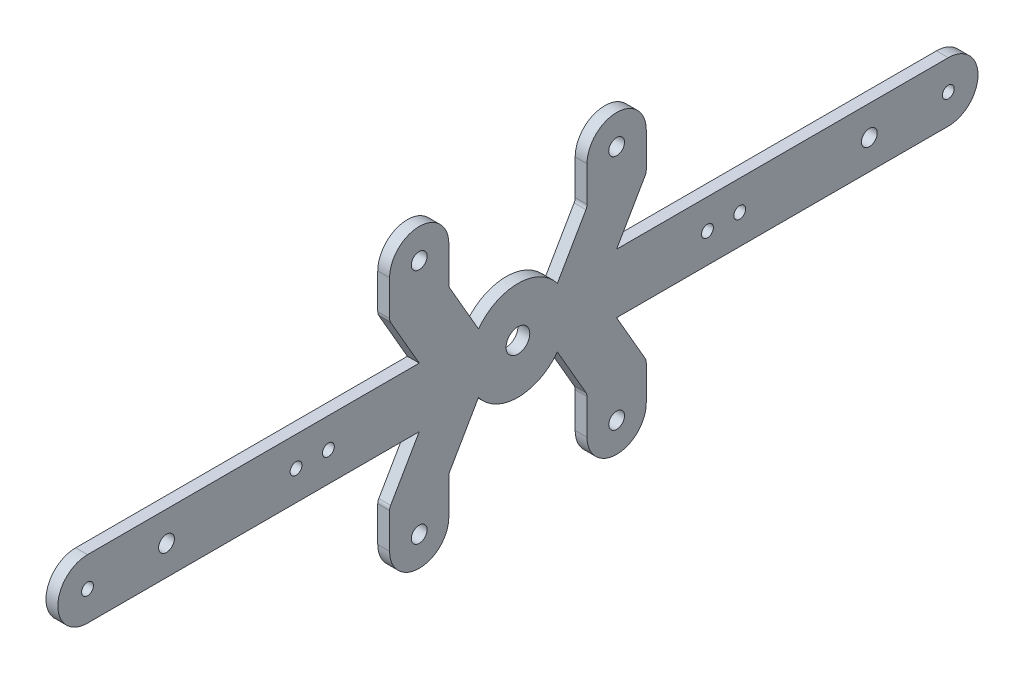
SolidWorks part; units mm, degrees
material "Acrylic (Medium-high impact)"
ref_plane "Front Plane" through (0, 0, 0) normal (0, 0, 1) x (1, 0, 0)
ref_plane "Top Plane" through (0, 0, 0) normal (0, 1, 0) x (1, 0, 0)
ref_plane "Right Plane" through (0, 0, 0) normal (1, 0, 0) x (0, 0, -1)
sketch "Sketch1" plane through (0, 0, 0) normal (1, 0, 0) x (0, 0, -1)
  line L0 (0, 0) -> (-114.2997, 0) construction
  line L1 (125, -45) -> (-125, -45)
  line L2 (125, -45) -> (125, 45)
  line L3 (125, 45) -> (-125, 45)
  line L4 (-125, -45) -> (-125, 45)
  line L5 (125, -45) -> (-125, 45) construction
  line L6 (125, 45) -> (-125, -45) construction
  point P0 (0, 0)
  dimension "D1" = 250
  dimension "D2" = 90
extrude "Boss-Extrude1" add sketch "Sketch1" along normal blind 3
sketch "Sketch2" plane through (3, 0, 0) normal (1, 0, 0) x (0, 0, -1)
  circle A0 centre (0, 0) radius 3
  circle A1 centre (-48, 0) radius 1.5
  circle A2 centre (-89, 0) radius 2
  circle A3 centre (-109, 0) radius 1.5
  circle A4 centre (-56.18, 0) radius 1.5
  dimension "D1" = 4
  dimension "D2" = 3
  dimension "D3" = 6
  dimension "D4" = 20
  dimension "D7" = 3
  dimension "D5" = 41
  dimension "D6" = 48
  dimension "D8" = 32.82
extrude "Cut-Extrude1" cut sketch "Sketch2" against normal through all
sketch "Sketch3" plane through (3, 0, 0) normal (1, 0, 0) x (0, 0, -1)
  line L0 (0, 55) -> (0, -55) construction
  line L1 (55, 0) -> (-55, 0) construction
  circle A0 centre (-25, 30) radius 2
  dimension "D1" = 4
  dimension "D2" = 25
  dimension "D3" = 30
extrude "Cut-Extrude2" cut sketch "Sketch3" against normal through all
sketch "Sketch4" plane through (3, 0, 0) normal (1, 0, 0) x (0, 0, -1)
  line L2 (-125, 1.9956) -> (-125, 45)
  line L5 (-125, 45) -> (0, 45)
  line L6 (125, 45) -> (-125, 45) construction
  line L13 (-116.5146, 0) -> (-125, 0)
  line L14 (-125, 45) -> (-125, -45) construction
  line L15 (-125, 0) -> (-125, 1.9956)
  line L20 (-32.5, 30) -> (-32.5, 20.5239)
  line L21 (-17.5, 30) -> (-17.5, 20.5239)
  line L23 (0, 45) -> (0, 12.5)
  line L29 (-9.989, 7.5146) -> (-17.5, 20.5239)
  line L30 (55, 0) -> (-55, 0) construction
  line L31 (-24.989, 7.5146) -> (-32.5, 20.5239)
  line L32 (-109, 7.5146) -> (-24.989, 7.5146)
  arc A7 (-17.5, 30) -> (-32.5, 30) centre (-25, 30) ccw
  arc A16 (-109, 7.5146) -> (-116.5146, 0) centre (-109, 0) ccw
  arc A17 (0, 12.5) -> (-9.989, 7.5146) centre (0, 0) ccw
  dimension "D1" = 25
  dimension "D2" = 15
  dimension "D3" = 60
extrude "Cut-Extrude3" cut sketch "Sketch4" against normal through all
mirror "Mirror1" about plane through (0, 0, 0) normal (0, 1, 0) of "Cut-Extrude2", "Cut-Extrude3"
mirror "Mirror2" about plane through (0, 0, 0) normal (0, 0, 1) of "Cut-Extrude1", "Mirror1", "Cut-Extrude2", "Cut-Extrude3"
fillet "Fillet2" radius 2 8 edges at (1.5, 20.5239, 32.5) (1.5, 20.5239, -32.5) (1.5, -20.5239, -32.5) (1.5, -20.5239, 32.5) (1.5, 20.5239, 17.5) (1.5, -20.5239, 17.5) (1.5, -20.5239, -17.5) (1.5, 20.5239, -17.5)
